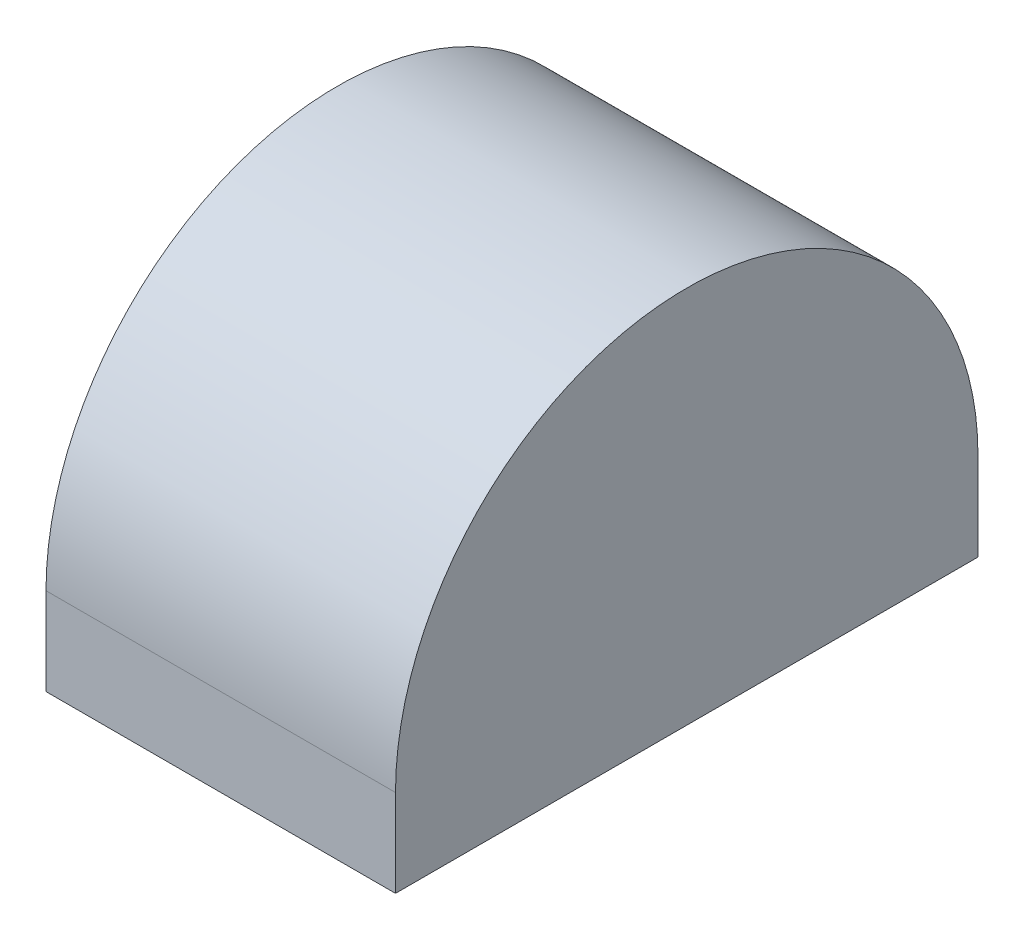
SolidWorks part; units mm, degrees
ref_plane "Front Plane" through (0, 0, 0) normal (0, 0, 1) x (1, 0, 0)
ref_plane "Top Plane" through (0, 0, 0) normal (0, 1, 0) x (1, 0, 0)
ref_plane "Right Plane" through (0, 0, 0) normal (1, 0, 0) x (0, 0, -1)
sketch "Sketch1" plane through (0, 0, 0) normal (1, 0, 0) x (0, 0, -1)
  line L0 (0, 0) -> (0, 3)
  line L1 (0, 0) -> (20, 0)
  line L2 (20, 0) -> (20, 3)
  arc A0 (0, 3) -> (20, 3) centre (10, 3) cw
  dimension "D1" = 3
  dimension "D2" = 20
extrude "Boss-Extrude1" add sketch "Sketch1" along normal mid plane 12
sketch "Sketch2" plane through (0, 0, 0) normal (1, 0, 0) x (0, 0, -1)
  line L0 (10, 0) -> (17.5, 0)
  line L1 (0, 0) -> (20, 0) construction
  line L2 (17.5, 0) -> (17.5, 3)
  line L3 (10, 0) -> (10, 11.5) construction
  line L4 (10, 11.5) -> (13.8888, 9.2548)
  line L5 (10, 11.5) -> (6.1112, 9.2548)
  line L6 (10, 0) -> (2.5, 0)
  line L7 (2.5, 0) -> (2.5, 3)
  line L8 (0, 3) -> (0, 0) construction
  arc A0 (20, 3) -> (0, 3) centre (10, 3) ccw construction
  arc A1 (2.5, 3) -> (6.1112, 9.2548) centre (9.7224, 3) cw
  arc A2 (13.8888, 9.2548) -> (17.5, 3) centre (10.2776, 3) cw
  point P13 (10, 13)
  dimension "D1" = 1.5
  dimension "D2" = 60
  dimension "D3" = 60
  dimension "D4" = 2.5
extrude "Cut-Extrude1" cut sketch "Sketch2" against normal mid plane 7
